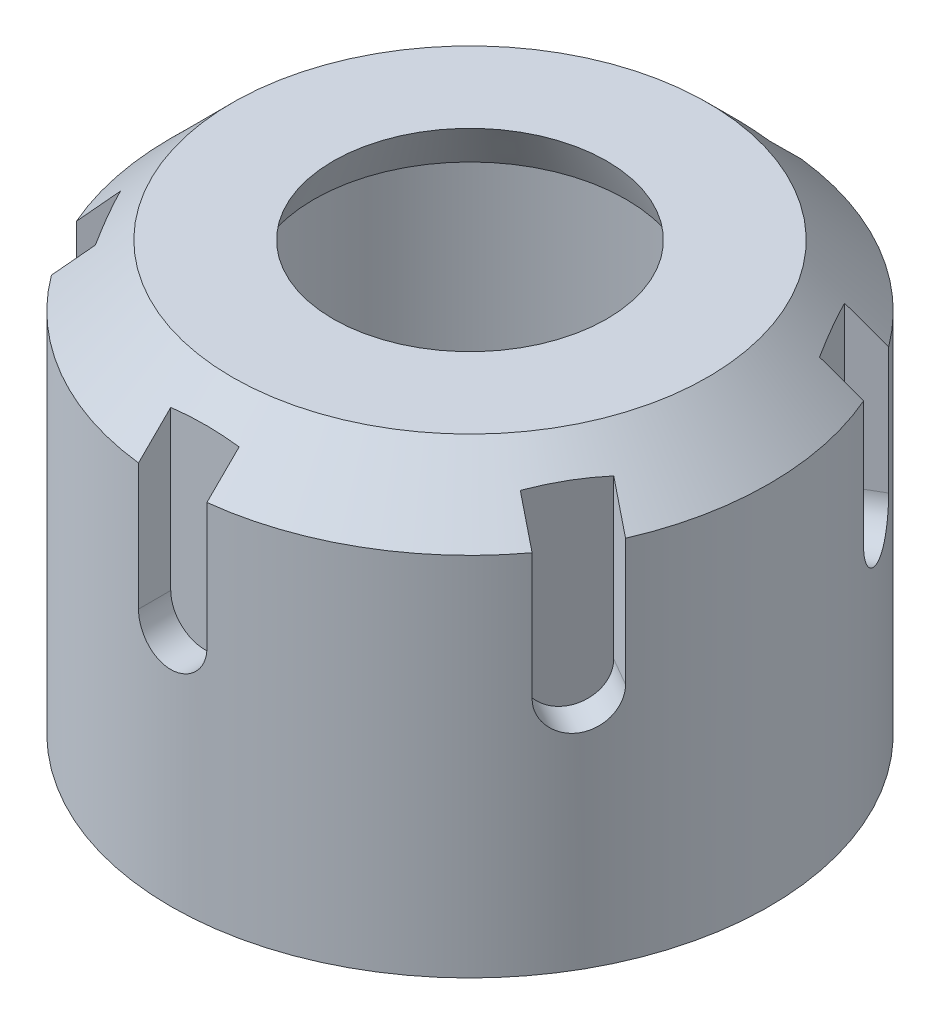
SolidWorks part; units mm, degrees
ref_plane "前视基准面" through (0, 0, 0) normal (0, 0, 1) x (1, 0, 0)
ref_plane "上视基准面" through (0, 0, 0) normal (0, 1, 0) x (1, 0, 0)
ref_plane "右视基准面" through (0, 0, 0) normal (1, 0, 0) x (0, 0, -1)
sketch "草图1" plane through (0, 0, 0) normal (0, 0, 1) x (1, 0, 0)
  line L0 (0, 88.5864) -> (0, -68.8309) construction
  line L1 (-16, 52.0383) -> (-27.8037, 52.0383)
  line L2 (-27.8037, 52.0383) -> (-35, 44.842)
  line L3 (-35, 44.842) -> (-35, 2.0383)
  line L4 (-35, 2.0383) -> (-30, 2.0383)
  line L5 (-18.2502, 47.0383) -> (-25.7326, 47.0383)
  line L6 (-25.7326, 47.0383) -> (-30, 42.7709)
  line L7 (-30, 42.7709) -> (-30, 2.0383)
  line L8 (-16, 52.0383) -> (-18.2502, 47.0383)
  line L9 (0, 52.0383) -> (-27.8037, 52.0383) construction
  line L10 (-35, 2.0383) -> (-44.6852, 2.0383) construction
  line L11 (-30, -2.9617) -> (-44.6852, -2.9617) construction
  line L12 (-30, 42.7709) -> (-30, -2.9617) construction
  line L13 (0, 47.0383) -> (-25.7326, 47.0383) construction
  dimension "D2" = 30
  dimension "D3" = 50
  dimension "D4" = 16
  dimension "D5" = 65.77
  dimension "D1" = 5
revolve "旋转1" add sketch "草图1" angle 360 about L0
cosmetic thread "装饰螺纹线1" parameters "D2"=64
ref_plane "基准面1" through (0, 0, 40) normal (0, 0, 1) x (1, 0, 0)
sketch "草图2" plane through (0, 0, 40) normal (0, 0, 1) x (1, 0, 0)
  line L0 (0, 74.1198) -> (0, 21.8531) construction
  line L1 (-4, 52.0383) -> (-4, 30.0383)
  line L2 (16, 52.0383) -> (-16, 52.0383) construction
  line L3 (4, 30.0383) -> (4, 52.0383)
  line L4 (-4, 52.0383) -> (4, 52.0383)
  arc A0 (-4, 30.0383) -> (4, 30.0383) centre (0, 30.0383) ccw
  dimension "D1" = 4
  dimension "D2" = 22
extrude "切除-拉伸4" cut sketch "草图2" against normal blind 9
pattern_circular "阵列(圆周)1" count 6 every 60 about axis through (0, 0, 0) along (0, 1, 0) of "切除-拉伸4"
